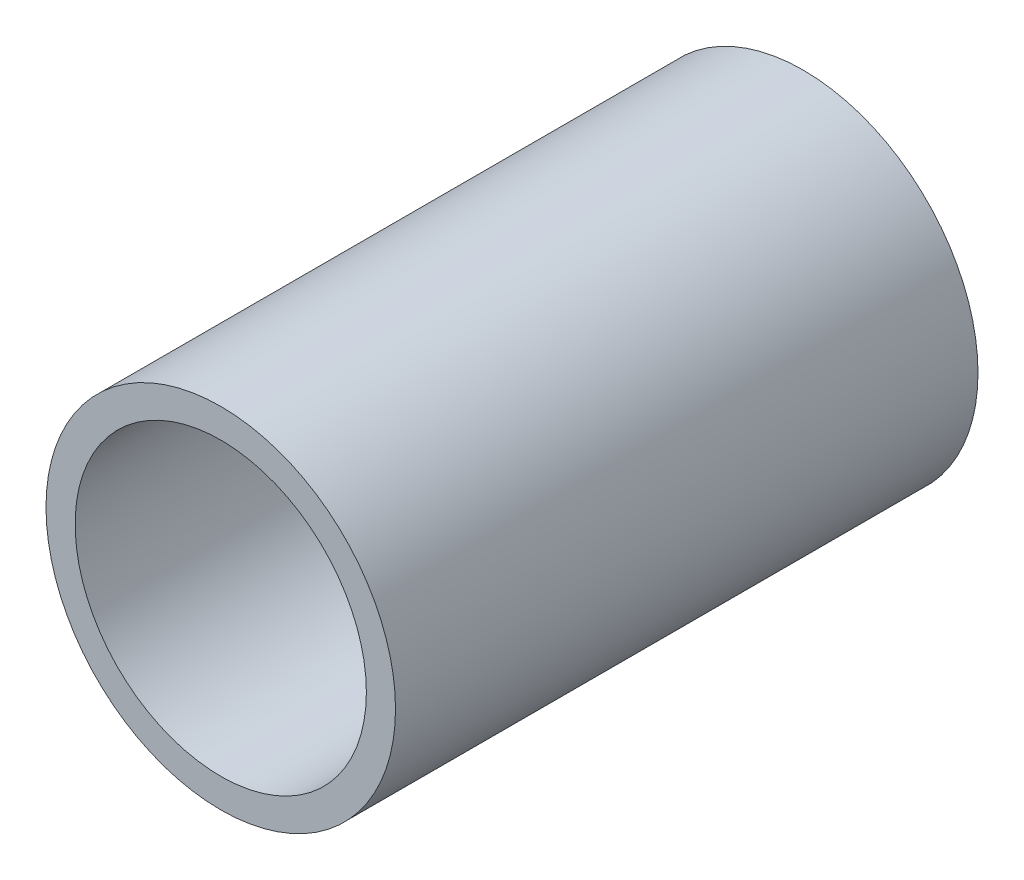
SolidWorks part; units mm, degrees
ref_plane "Front Plane" through (0, 0, 0) normal (0, 0, 1) x (1, 0, 0)
ref_plane "Top Plane" through (0, 0, 0) normal (0, 1, 0) x (1, 0, 0)
ref_plane "Right Plane" through (0, 0, 0) normal (1, 0, 0) x (0, 0, -1)
sketch "Sketch1" plane through (0, 0, 0) normal (0, 0, 1) x (1, 0, 0)
  circle A0 centre (0, 0) radius 25
  circle A1 centre (0, 0) radius 30
  dimension "D1" = 50
  dimension "D2" = 60
extrude "Boss-Extrude1" add sketch "Sketch1" along normal blind 100
